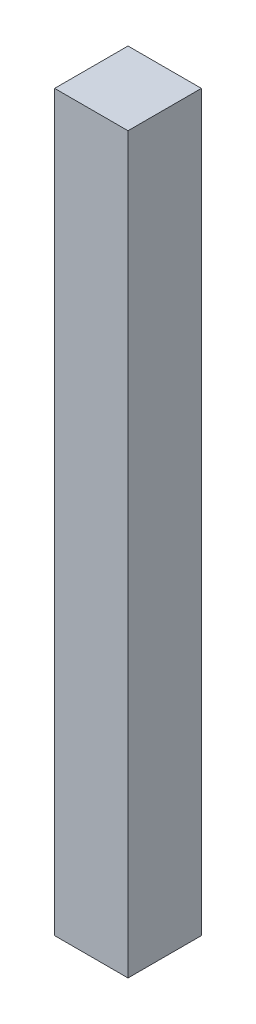
SolidWorks part; units mm, degrees
ref_plane "Plano frontal" through (0, 0, 0) normal (0, 0, 1) x (1, 0, 0)
ref_plane "Plano superior" through (0, 0, 0) normal (0, 1, 0) x (1, 0, 0)
ref_plane "Plano direito" through (0, 0, 0) normal (1, 0, 0) x (0, 0, -1)
sketch "Esboço2" plane through (0, 0, 0) normal (0, 1, 0) x (1, 0, 0)
  line L1 (-50, 29.0761) -> (0, 29.0761)
  line L2 (-50, 29.0761) -> (-50, -20.9239)
  line L3 (-50, -20.9239) -> (0, -20.9239)
  line L4 (0, 29.0761) -> (0, -20.9239)
  dimension "D1" = 50
  dimension "D2" = 50
extrude "Ressalto-extrusão1" add sketch "Esboço2" along normal blind 500 contours L1 L4 L3 L2
